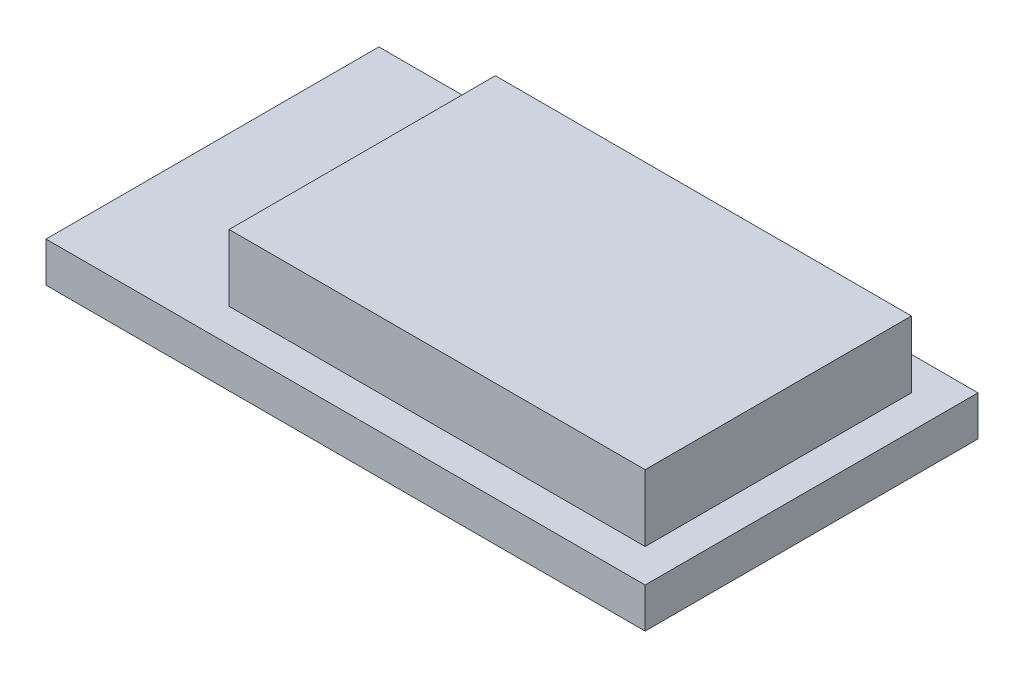
SolidWorks part; units mm, degrees
ref_plane "Front Plane" through (0, 0, 0) normal (0, 0, 1) x (1, 0, 0)
ref_plane "Top Plane" through (0, 0, 0) normal (0, 1, 0) x (1, 0, 0)
ref_plane "Right Plane" through (0, 0, 0) normal (1, 0, 0) x (0, 0, -1)
sketch "Sketch1" plane through (0, 0, 0) normal (0, 1, 0) x (1, 0, 0)
  line L1 (9, 5) -> (-9, 5)
  line L2 (9, 5) -> (9, -5)
  line L3 (9, -5) -> (-9, -5)
  line L4 (-9, 5) -> (-9, -5)
  line L5 (9, 5) -> (-9, -5) construction
  line L6 (9, -5) -> (-9, 5) construction
  point P0 (0, 0)
  dimension "D1" = 18
  dimension "D2" = 10
extrude "Boss-Extrude1" add sketch "Sketch1" against normal blind 1.2
sketch "Sketch2" plane through (0, 0, 0) normal (0, 1, 0) x (1, 0, 0)
  line L6 (-4.5, 4) -> (-4.5, -4)
  line L7 (-9, 5) -> (-9, -5) construction
  line L9 (-9, -4) -> (8, -4)
  line L10 (8, -4) -> (8, 4)
  line L11 (8, 4) -> (-9, 4)
  line L12 (-4.5, -4) -> (8, -4)
  line L13 (8, -4) -> (8, 4)
  line L14 (8, 4) -> (-4.5, 4)
  dimension "D2" = 4.5
  dimension "D1" = 1
extrude "Boss-Extrude2" add sketch "Sketch2" along normal blind 2
